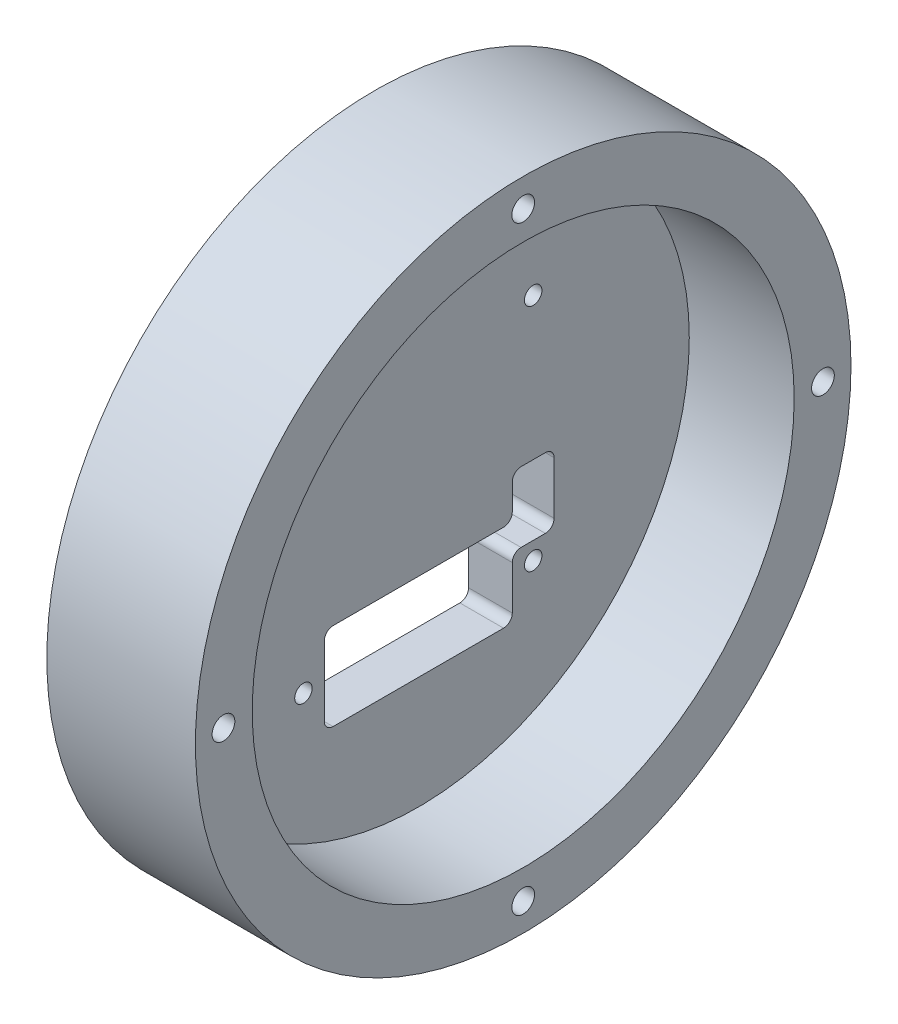
SolidWorks part; units mm, degrees
ref_plane "Front Plane" through (0, 0, 0) normal (0, 0, 1) x (1, 0, 0)
ref_plane "Top Plane" through (0, 0, 0) normal (0, 1, 0) x (1, 0, 0)
ref_plane "Right Plane" through (0, 0, 0) normal (1, 0, 0) x (0, 0, -1)
sketch "Sketch1" plane through (0, 0, 0) normal (1, 0, 0) x (0, 0, -1)
  circle A0 centre (0, 0) radius 37.5
  dimension "D1" = 75
extrude "Boss-Extrude1" add sketch "Sketch1" along normal blind 5
sketch "Sketch3" plane through (0, 0, 0) normal (-1, 0, 0) x (0, 0, 1)
  circle A0 centre (-13.14, 13.14) radius 1
  circle A1 centre (13.14, 13.14) radius 1
  circle A2 centre (13.14, -13.14) radius 1
  circle A3 centre (-13.14, -13.14) radius 1
  point P12 (0, 0)
  dimension "D1" = 2
  dimension "D2" = 13.14
  dimension "D3" = 13.14
  dimension "D4" = 4
extrude "Cut-Extrude2" cut sketch "Sketch3" against normal through all
sketch "Sketch4" plane through (5, 0, 0) normal (1, 0, 0) x (0, 0, -1)
  circle A0 centre (0, 0) radius 37.5
  circle A1 centre (0, 0) radius 31
  dimension "D1" = 75
  dimension "D2" = 62
extrude "Boss-Extrude2" add sketch "Sketch4" along normal blind 12
sketch "Sketch2" plane through (5, 0, 0) normal (1, 0, 0) x (0, 0, -1)
  line L0 (0, 34.29) -> (0, 37.5) construction
  circle A1 centre (0, 34.29) radius 1.3
  circle A3 centre (0, 0) radius 37.5 construction
  circle A8 centre (34.29, 0) radius 1.3
  circle A9 centre (0, -34.29) radius 1.3
  circle A10 centre (-34.29, 0) radius 1.3
  point P16 (0, 0)
  dimension "D2" = 2.6
  dimension "D1" = 34.29
  dimension "D3" = 4
extrude "Cut-Extrude1" cut sketch "Sketch2" against normal through all both and the other way through all
sketch "Sketch5" plane through (5, 0, 0) normal (1, 0, 0) x (0, 0, -1)
  line L0 (-13.14, -13.14) -> (13.14, -13.14) construction
  line L1 (9.75, -8.14) -> (-9.75, -8.14)
  line L2 (10.75, -12.14) -> (10.75, -17.14)
  line L3 (9.75, -18.14) -> (-9.75, -18.14)
  line L4 (-10.75, -9.14) -> (-10.75, -17.14)
  line L5 (10.75, -8.14) -> (-10.75, -18.14) construction
  line L6 (10.75, -18.14) -> (-10.75, -8.14) construction
  line L8 (14.53, -3.14) -> (11.75, -3.14)
  line L9 (15.53, -4.14) -> (15.53, -10.14)
  line L10 (14.53, -11.14) -> (11.75, -11.14)
  line L11 (10.75, -4.14) -> (10.75, -7.14)
  line L12 (15.53, -3.14) -> (10.75, -11.14) construction
  line L13 (15.53, -11.14) -> (10.75, -3.14) construction
  arc A0 (11.75, -11.14) -> (10.75, -12.14) centre (11.75, -12.14) ccw
  arc A1 (-10.75, -9.14) -> (-9.75, -8.14) centre (-9.75, -9.14) cw
  arc A2 (-9.75, -18.14) -> (-10.75, -17.14) centre (-9.75, -17.14) cw
  arc A3 (10.75, -17.14) -> (9.75, -18.14) centre (9.75, -17.14) cw
  arc A4 (15.53, -10.14) -> (14.53, -11.14) centre (14.53, -10.14) cw
  arc A5 (10.75, -4.14) -> (11.75, -3.14) centre (11.75, -4.14) cw
  arc A6 (15.53, -4.14) -> (14.53, -3.14) centre (14.53, -4.14) ccw
  arc A7 (9.75, -8.14) -> (10.75, -7.14) centre (9.75, -7.14) ccw
  point P0 (0, -13.14)
  point P5 (13.14, -7.14)
  dimension "D5" = 1
  dimension "D6" = 1
  dimension "D1" = 10
  dimension "D2" = 21.5
  dimension "D3" = 8
  dimension "D4" = 2
extrude "Cut-Extrude3" cut sketch "Sketch5" against normal through all
sketch "Sketch6" plane through (0, 0, 0) normal (-1, 0, 0) x (0, 0, 1)
  line L0 (0, 37.5) -> (0, -37.5) construction
  line L1 (-18.75, 32.476) -> (18.75, -32.476) construction
  line L2 (-18.75, 32.476) -> (-17.145, 29.696) construction
  line L3 (17.145, -29.696) -> (18.75, -32.476) construction
  circle A0 centre (0, 0) radius 37.5 construction
  circle A1 centre (-17.145, 29.696) radius 1.5
  circle A2 centre (17.145, -29.696) radius 1.5
  circle A3 centre (29.696, 17.145) radius 1.5
  circle A4 centre (17.145, -29.696) radius 1.5 [skipped]
  circle A5 centre (-29.696, -17.145) radius 1.5
  point P7 (0, 0)
  point P22 (0, 0)
  dimension "D2" = 3
  dimension "D3" = 3
  dimension "D4" = 68.58
  dimension "D1" = 30
  dimension "D5" = 4
extrude "Cut-Extrude4" [suppressed] cut sketch "Sketch6" against normal through all
